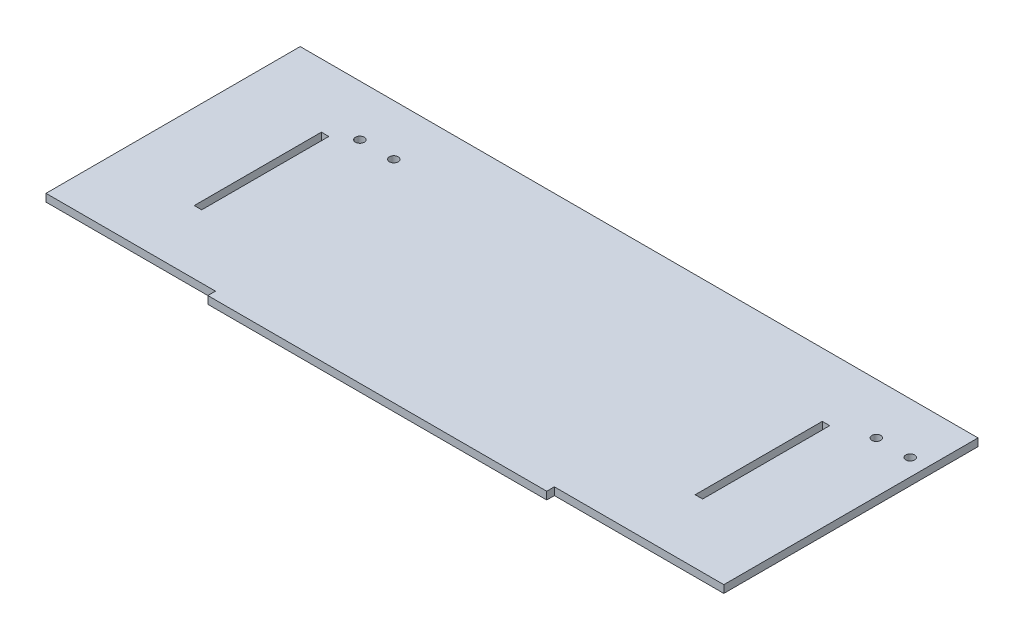
SolidWorks part; units mm, degrees
ref_plane "Front Plane" through (0, 0, 0) normal (0, 0, 1) x (1, 0, 0)
ref_plane "Top Plane" through (0, 0, 0) normal (0, 1, 0) x (1, 0, 0)
ref_plane "Right Plane" through (0, 0, 0) normal (1, 0, 0) x (0, 0, -1)
sketch "Sketch1" plane through (0, 0, 0) normal (0, 1, 0) x (1, 0, 0)
  line L1 (-200, 75) -> (200, 75)
  line L2 (-200, 75) -> (-200, -75)
  line L3 (-200, -75) -> (200, -75)
  line L4 (200, 75) -> (200, -75)
  line L5 (-200, 75) -> (200, -75) construction
  line L6 (-200, -75) -> (200, 75) construction
  line L7 (-100, -70.5) -> (100, -70.5)
  line L8 (-100, -70.5) -> (-100, -79.5)
  line L9 (-100, -79.5) -> (100, -79.5)
  line L10 (100, -70.5) -> (100, -79.5)
  line L11 (-100, -70.5) -> (100, -79.5) construction
  line L12 (-100, -79.5) -> (100, -70.5) construction
  point P0 (0, 0)
  point P5 (0, -75)
  dimension "D1" = 400
  dimension "D2" = 200
  dimension "D3" = 9
  dimension "D4" = 150
extrude "Boss-Extrude1" add sketch "Sketch1" along normal blind 4.5 contours L7 L10 L3 L4 L1 L2 L8 | L10 L3 L8 L9 | L10 L7 L8 L3
sketch "Sketch3" plane through (0, 4.5, 0) normal (0, 1, 0) x (1, 0, 0)
  line L0 (-55, 0) -> (55, 0) construction
  line L1 (-150, -37.5) -> (-145.6, -37.5)
  line L2 (-150, -37.5) -> (-150, 37.5)
  line L3 (-150, 37.5) -> (-145.6, 37.5)
  line L4 (-145.6, -37.5) -> (-145.6, 37.5)
  line L5 (-150, -37.5) -> (-145.6, 37.5) construction
  line L6 (-150, 37.5) -> (-145.6, -37.5) construction
  line L7 (-200, 75) -> (-200, -75) construction
  point P0 (-147.8, 0)
  dimension "D1" = 75
  dimension "D2" = 4.4
  dimension "D3" = 50
extrude "Cut-Extrude1" cut sketch "Sketch3" against normal up to surface (4.5 mm away) contours L2 L3 L4 L1 up to face at (0, 0, 38.625)
mirror "Mirror1" about plane through (0, 0, 0) normal (1, 0, 0) of "Cut-Extrude1"
sketch "Sketch5" plane through (0, 4.5, 0) normal (0, 1, 0) x (1, 0, 0)
  line L0 (-2.475, 0) -> (2.475, 0) construction
  line L3 (170, 45) -> (-114.7779, 45) construction
  line L10 (-134.7779, 45) -> (-114.7779, 45) construction
  line L11 (170, 45) -> (190, 45) construction
  line L12 (-200, 75) -> (200, 75) construction
  circle A0 centre (-114.7779, 45) radius 2.6
  circle A1 centre (170, 45) radius 2.6
  circle A2 centre (-134.7779, 45) radius 2.6
  circle A3 centre (190, 45) radius 2.6
  point P0 (32.2, 0)
  dimension "D3" = 20
  dimension "D5" = 5.2
  dimension "D1" = 284.7779
  dimension "D2" = 20
  dimension "D4" = 30
extrude "Cut-Extrude2" cut sketch "Sketch5" against normal up to next
